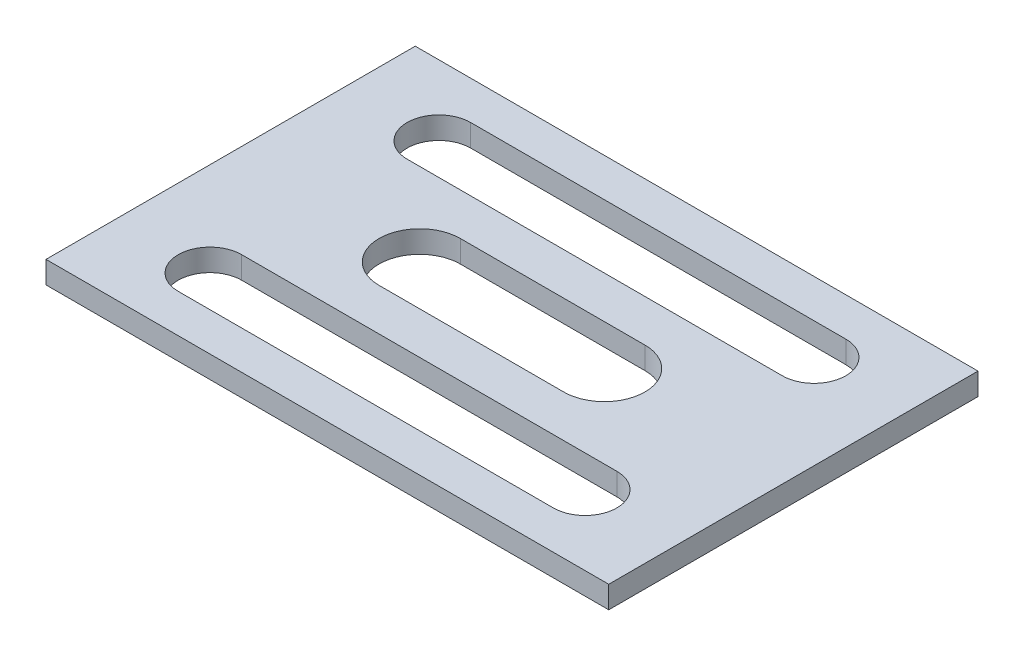
SolidWorks part; units mm, degrees
ref_plane "Front Plane" through (0, 0, 0) normal (0, 0, 1) x (1, 0, 0)
ref_plane "Top Plane" through (0, 0, 0) normal (0, 1, 0) x (1, 0, 0)
ref_plane "Right Plane" through (0, 0, 0) normal (1, 0, 0) x (0, 0, -1)
sketch "Sketch1" plane through (0, 0, 0) normal (0, 1, 0) x (1, 0, 0)
  line L1 (-38.1, 25) -> (38.1, 25)
  line L2 (-38.1, 25) -> (-38.1, -25)
  line L3 (-38.1, -25) -> (38.1, -25)
  line L4 (38.1, 25) -> (38.1, -25)
  line L5 (-38.1, 25) -> (38.1, -25) construction
  line L6 (-38.1, -25) -> (38.1, 25) construction
  point P0 (0, 0)
  dimension "D1" = 50
  dimension "D2" = 76.2
extrude "Boss-Extrude1" add sketch "Sketch1" along normal blind 3
sketch "Sketch2" plane through (0, 3, 0) normal (0, 1, 0) x (1, 0, 0)
  line L0 (-25.4, 15.5) -> (25.4, 15.5) construction
  line L1 (-15.5, 15.5) -> (15.5, 15.5) construction
  line L2 (-15.5, 15.5) -> (-15.5, -15.5) construction
  line L3 (-15.5, -15.5) -> (15.5, -15.5) construction
  line L4 (15.5, 15.5) -> (15.5, -15.5) construction
  line L5 (-15.5, 15.5) -> (15.5, -15.5) construction
  line L6 (-15.5, -15.5) -> (15.5, 15.5) construction
  line L7 (-25.4, 19.8) -> (25.4, 19.8)
  line L8 (-25.4, 11.2) -> (25.4, 11.2)
  line L9 (0, 0) -> (15.5, 0) construction
  line L10 (-25.4, -15.5) -> (25.4, -15.5) construction
  line L11 (-25.4, -19.8) -> (25.4, -19.8)
  line L12 (-25.4, -11.2) -> (25.4, -11.2)
  line L13 (-12.5, 0) -> (12.5, 0) construction
  line L14 (-12.5, 5.5) -> (12.5, 5.5)
  line L15 (-12.5, -5.5) -> (12.5, -5.5)
  arc A0 (-25.4, 19.8) -> (-25.4, 11.2) centre (-25.4, 15.5) ccw
  arc A1 (25.4, 11.2) -> (25.4, 19.8) centre (25.4, 15.5) ccw
  arc A2 (-25.4, -19.8) -> (-25.4, -11.2) centre (-25.4, -15.5) cw
  arc A3 (25.4, -11.2) -> (25.4, -19.8) centre (25.4, -15.5) cw
  arc A4 (-12.5, 5.5) -> (-12.5, -5.5) centre (-12.5, 0) ccw
  arc A5 (12.5, -5.5) -> (12.5, 5.5) centre (12.5, 0) ccw
  point P0 (0, 0)
  point P8 (0, 15.5)
  point P17 (0, -15.5)
  point P24 (0, 0)
  dimension "D3" = 4.3
  dimension "D6" = 5.5
  dimension "D1" = 31
  dimension "D2" = 31
  dimension "D4" = 50.8
  dimension "D5" = 25
extrude "Cut-Extrude1" cut sketch "Sketch2" against normal through all
